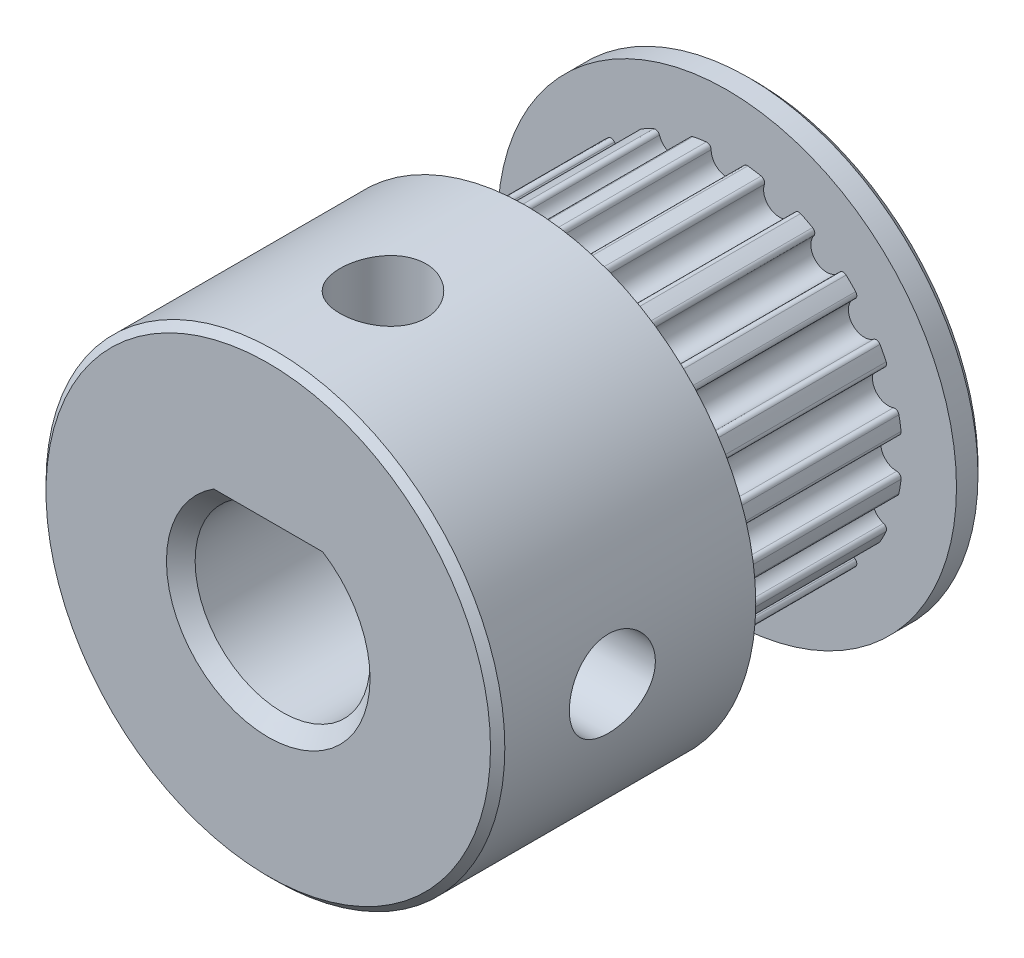
SolidWorks part; units mm, degrees
ref_plane "Front Plane" through (0, 0, 0) normal (0, 0, 1) x (1, 0, 0)
ref_plane "Top Plane" through (0, 0, 0) normal (0, 1, 0) x (1, 0, 0)
ref_plane "Right Plane" through (0, 0, 0) normal (1, 0, 0) x (0, 0, -1)
sketch "Sketch1" plane through (0, 0, 0) normal (0, 1, 0) x (1, 0, 0)
  line L0 (8, 1) -> (0, 1)
  line L1 (0, 1) -> (0, 0)
  line L2 (0, 0) -> (8, 0)
  line L3 (8, 0) -> (8, 1)
  line L4 (0, 1) -> (0, 0) construction
revolve "Revolve1" add sketch "Sketch1" angle 360 about L4
sketch "Sketch2" plane through (0, 0, 0) normal (0, 0, 1) x (1, 0, 0)
  arc A0 (0.5276, -6.0872) -> (-0.5276, -6.0872) centre (0, -5.915) ccw
  arc A1 (-0.5276, -6.0872) -> (-1.3792, -5.9523) centre (0, 0) cw
  arc A2 (-1.3792, -5.9523) -> (-2.3828, -5.6262) centre (-1.8278, -5.6255) ccw
  arc A3 (-2.3828, -5.6262) -> (-3.1511, -5.2348) centre (0, 0) cw
  arc A4 (-3.1511, -5.2348) -> (-4.0048, -4.6145) centre (-3.4767, -4.7853) ccw
  arc A5 (-4.0048, -4.6145) -> (-4.6145, -4.0048) centre (0, 0) cw
  arc A6 (-4.6145, -4.0048) -> (-5.2348, -3.1511) centre (-4.7853, -3.4767) ccw
  arc A7 (-5.2348, -3.1511) -> (-5.6262, -2.3828) centre (0, 0) cw
  arc A8 (-5.6262, -2.3828) -> (-5.9523, -1.3792) centre (-5.6255, -1.8278) ccw
  arc A9 (-5.9523, -1.3792) -> (-6.0872, -0.5276) centre (0, 0) cw
  arc A10 (-6.0872, -0.5276) -> (-6.0872, 0.5276) centre (-5.915, 0) ccw
  arc A11 (-6.0872, 0.5276) -> (-5.9523, 1.3792) centre (0, 0) cw
  arc A12 (-5.9523, 1.3792) -> (-5.6262, 2.3828) centre (-5.6255, 1.8278) ccw
  arc A13 (-5.6262, 2.3828) -> (-5.2348, 3.1511) centre (0, 0) cw
  arc A14 (-5.2348, 3.1511) -> (-4.6145, 4.0048) centre (-4.7853, 3.4767) ccw
  arc A15 (-4.6145, 4.0048) -> (-4.0048, 4.6145) centre (0, 0) cw
  arc A16 (-4.0048, 4.6145) -> (-3.1511, 5.2348) centre (-3.4767, 4.7853) ccw
  arc A17 (-3.1511, 5.2348) -> (-2.3828, 5.6262) centre (0, 0) cw
  arc A18 (-2.3828, 5.6262) -> (-1.3792, 5.9523) centre (-1.8278, 5.6255) ccw
  arc A19 (-1.3792, 5.9523) -> (-0.5276, 6.0872) centre (0, 0) cw
  arc A20 (-0.5276, 6.0872) -> (0.5276, 6.0872) centre (0, 5.915) ccw
  arc A21 (0.5276, 6.0872) -> (1.3792, 5.9523) centre (0, 0) cw
  arc A22 (1.3792, 5.9523) -> (2.3828, 5.6262) centre (1.8278, 5.6255) ccw
  arc A23 (2.3828, 5.6262) -> (3.1511, 5.2348) centre (0, 0) cw
  arc A24 (3.1511, 5.2348) -> (4.0048, 4.6145) centre (3.4767, 4.7853) ccw
  arc A25 (4.0048, 4.6145) -> (4.6145, 4.0048) centre (0, 0) cw
  arc A26 (4.6145, 4.0048) -> (5.2348, 3.1511) centre (4.7853, 3.4767) ccw
  arc A27 (5.2348, 3.1511) -> (5.6262, 2.3828) centre (0, 0) cw
  arc A28 (5.6262, 2.3828) -> (5.9523, 1.3792) centre (5.6255, 1.8278) ccw
  arc A29 (5.9523, 1.3792) -> (6.0872, 0.5276) centre (0, 0) cw
  arc A30 (6.0872, 0.5276) -> (6.0872, -0.5276) centre (5.915, 0) ccw
  arc A31 (6.0872, -0.5276) -> (5.9523, -1.3792) centre (0, 0) cw
  arc A32 (5.9523, -1.3792) -> (5.6262, -2.3828) centre (5.6255, -1.8278) ccw
  arc A33 (5.6262, -2.3828) -> (5.2348, -3.1511) centre (0, 0) cw
  arc A34 (5.2348, -3.1511) -> (4.6145, -4.0048) centre (4.7853, -3.4767) ccw
  arc A35 (4.6145, -4.0048) -> (4.0048, -4.6145) centre (0, 0) cw
  arc A36 (4.0048, -4.6145) -> (3.1511, -5.2348) centre (3.4767, -4.7853) ccw
  arc A37 (3.1511, -5.2348) -> (2.3828, -5.6262) centre (0, 0) cw
  arc A38 (2.3828, -5.6262) -> (1.3792, -5.9523) centre (1.8278, -5.6255) ccw
  arc A39 (1.3792, -5.9523) -> (0.5276, -6.0872) centre (0, 0) cw
extrude "Boss-Extrude1" add sketch "Sketch2" along normal blind 7
ref_plane "Plane1" through (0, 0, 7) normal (0, 0, -1) x (-1, 0, 0)
sketch "Sketch3" plane through (0, 0, 7) normal (0, 0, -1) x (-1, 0, 0)
  circle A0 centre (0, 0) radius 8
extrude "Boss-Extrude2" add sketch "Sketch3" against normal blind 9
sketch "Sketch4" plane through (0, 0, 16) normal (0, 0, 1) x (1, 0, 0)
  line L0 (1.7471, 2.5) -> (-1.7471, 2.5)
  arc A0 (-1.7471, 2.5) -> (1.7471, 2.5) centre (0, 0) ccw
extrude "Cut-Extrude1" cut sketch "Sketch4" against normal through all
hole_wizard "Ø3.0 Diameter Hole1" positions "3DSketch1" profile "Sketch5" hole size "Ø3.0" standard "ANSI Metric"
sketch3d "3DSketch1"
  point P0 (8, 0, 12)
sketch "Sketch5" plane through (8, 0, 12) normal (0, 1, 0) x (0, 0, -1)
  line L0 (0, 0) -> (0, 4.95)
  line L1 (0, 4.95) -> (1.5, 4.95)
  line L2 (1.5, 4.95) -> (1.5, 0)
  line L5 (1.5, 0) -> (0, 0)
  line L11 (0, -6.35) -> (0, 107.95) construction
  dimension "Thru Hole Dia." = 3
  dimension "Thru Hole Depth" = 4.95
hole_wizard "Ø3.0) Diameter Hole2" positions "Sketch7" profile "Sketch6" hole size "Ø3.0" standard "ANSI Metric"
sketch "Sketch7" plane through (0, 2.5, 0) normal (0, -1, 0) x (-1, 0, 0)
  point P0 (0, -12)
sketch "Sketch6" plane through (0, 2.5, 12) normal (1, 0, 0) x (0, 0, -1)
  line L0 (0, 0) -> (0, 5.5)
  line L1 (0, 5.5) -> (1.5, 5.5)
  line L2 (1.5, 5.5) -> (1.5, 0)
  line L5 (1.5, 0) -> (0, 0)
  line L11 (0, -6.35) -> (0, 107.95) construction
  dimension "Thru Hole Dia." = 3
  dimension "Thru Hole Depth" = 5.5
chamfer "Chamfer1" distance 0.25 angle 45 2 edges at (8, 0, 16) (8, 0, -1)
chamfer "Chamfer2" distance 0.5 angle 45 4 edges at (0, 2.5, -1) (0, -3.05, -1) (0, -3.05, 16) (0, 2.5, 16)
fillet "Fillet1" radius 0.15 40 edges at (-5.9523, 1.3792, 3.5) (-3.1511, -5.2348, 3.5) (-0.5276, 6.0872, 3.5) (1.3792, 5.9523, 3.5) (-5.6262, -2.3828, 3.5) (2.3828, 5.6262, 3.5) (-4.0048, 4.6145, 3.5) (0.5276, 6.0872, 3.5) (-1.3792, -5.9523, 3.5) (3.1511, 5.2348, 3.5) (-4.6145, -4.0048, 3.5) (4.0048, 4.6145, 3.5) (-6.0872, -0.5276, 3.5) (4.6145, 4.0048, 3.5) (-5.2348, 3.1511, 3.5) (5.2348, 3.1511, 3.5) (-2.3828, 5.6262, 3.5) (5.6262, 2.3828, 3.5) (-0.5276, -6.0872, 3.5) (5.9523, 1.3792, 3.5) (-2.3828, -5.6262, 3.5) (6.0872, 0.5276, 3.5) (-4.0048, -4.6145, 3.5) (6.0872, -0.5276, 3.5) (-5.2348, -3.1511, 3.5) (5.9523, -1.3792, 3.5) (-5.9523, -1.3792, 3.5) (5.6262, -2.3828, 3.5) (-6.0872, 0.5276, 3.5) (5.2348, -3.1511, 3.5) (-5.6262, 2.3828, 3.5) (4.6145, -4.0048, 3.5) (-4.6145, 4.0048, 3.5) (4.0048, -4.6145, 3.5) (-3.1511, 5.2348, 3.5) (2.3828, -5.6262, 3.5) (-1.3792, 5.9523, 3.5) (1.3792, -5.9523, 3.5) (0.5276, -6.0872, 3.5) (3.1511, -5.2348, 3.5)
